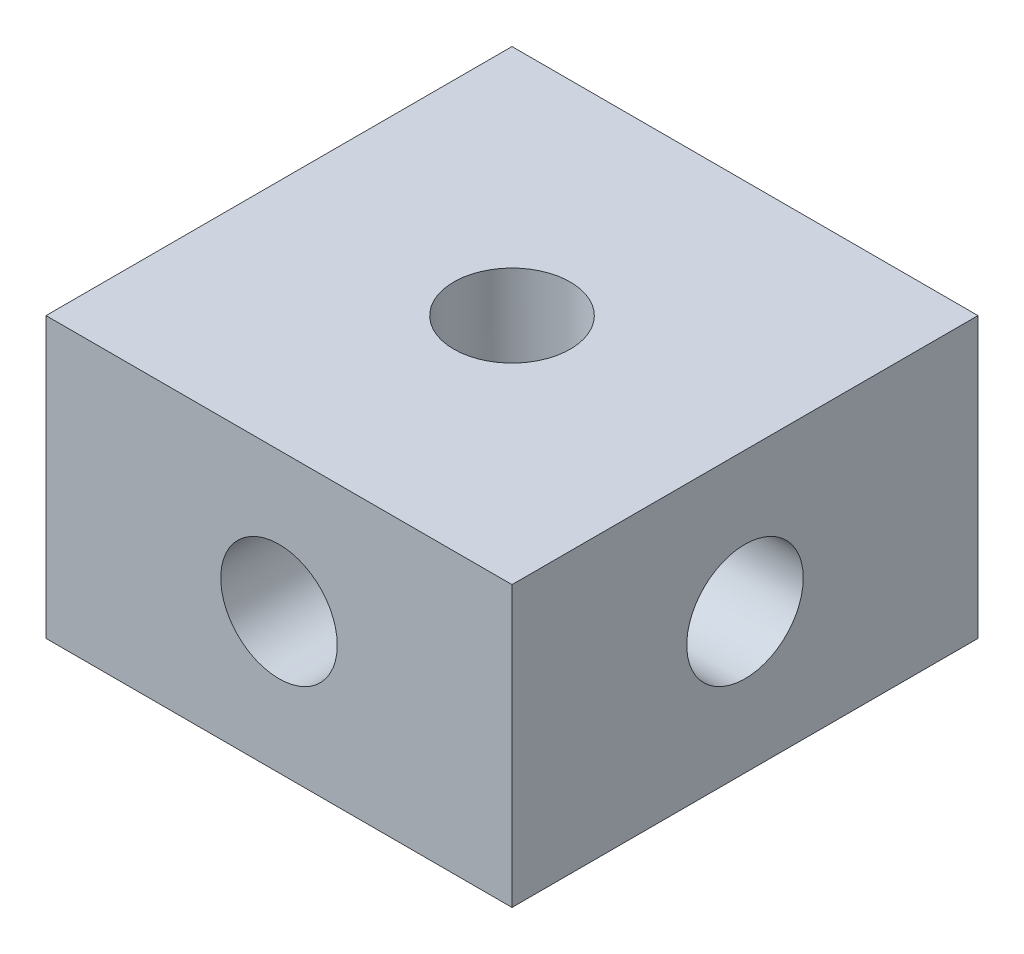
SolidWorks part; units mm, degrees
material "6061 合金"
ref_plane "前基準面" through (0, 0, 0) normal (0, 0, 1) x (1, 0, 0)
ref_plane "上基準面" through (0, 0, 0) normal (0, 1, 0) x (1, 0, 0)
ref_plane "右基準面" through (0, 0, 0) normal (1, 0, 0) x (0, 0, -1)
sketch "草圖1" plane through (0, 0, 0) normal (0, 1, 0) x (1, 0, 0)
  line L1 (-5, -5) -> (5, -5)
  line L2 (-5, -5) -> (-5, 5)
  line L3 (-5, 5) -> (5, 5)
  line L4 (5, -5) -> (5, 5)
  line L5 (0, 5) -> (0, -5) construction
  line L6 (-5, 0) -> (5, 0) construction
  point P0 (0, 0)
  dimension "D1" = 10
extrude "填料-伸長1" add sketch "草圖1" along normal mid plane 6
sketch "草圖2" plane through (0, 3, 0) normal (0, 1, 0) x (1, 0, 0)
  circle A0 centre (0, 0) radius 1.25
  dimension "D1" = 2.5
extrude "除料-伸長1" cut sketch "草圖2" against normal through all
cosmetic thread "裝飾螺紋線1" parameters "D2"=3
sketch "草圖3" plane through (0, 0, 5) normal (0, 0, 1) x (1, 0, 0)
  circle A0 centre (0, 0) radius 1.25
  dimension "D1" = 2.5
extrude "除料-伸長2" cut sketch "草圖3" against normal through all
cosmetic thread "裝飾螺紋線2" parameters "D2"=3
sketch "草圖4" plane through (5, 0, 0) normal (1, 0, 0) x (0, 0, -1)
  circle A0 centre (0, 0) radius 1.25
  dimension "D1" = 2.5
extrude "除料-伸長3" cut sketch "草圖4" against normal through all
cosmetic thread "裝飾螺紋線3" parameters "D2"=3
